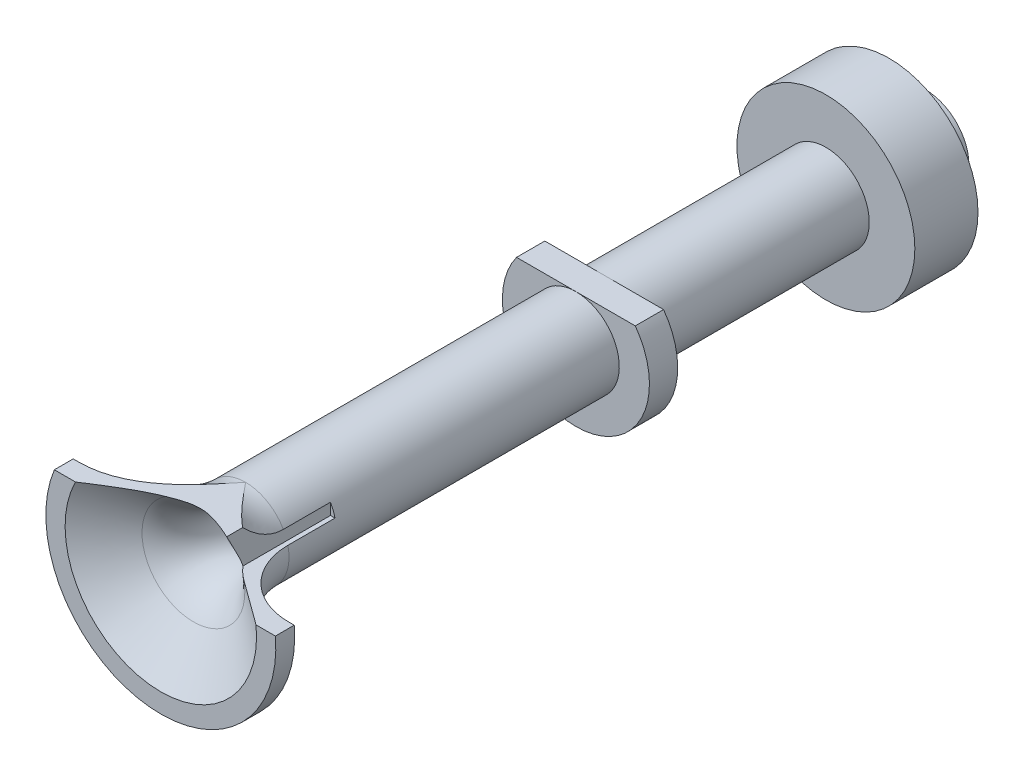
SolidWorks part; units mm, degrees
ref_plane "Спереди" through (0, 0, 0) normal (0, 0, 1) x (1, 0, 0)
ref_plane "Сверху" through (0, 0, 0) normal (0, 1, 0) x (1, 0, 0)
ref_plane "Справа" through (0, 0, 0) normal (1, 0, 0) x (0, 0, -1)
other "Configuration Table"
sketch "Sketch1" plane through (0, 0, 0) normal (1, 0, 0) x (0, 0, -1)
  line L0 (0, 0) -> (15.3, 0) construction
  line L1 (19.1862, 5.0782) -> (19.1862, 6.1)
  line L4 (19.1862, 6.1) -> (20.1862, 6.1)
  line L5 (20.1862, 6.1) -> (20.1862, 5.8)
  line L6 (20.9151, 2.7267) -> (19.1862, 5.0782)
  line L7 (59.7578, 1.3) -> (23.7349, 1.3)
  line L9 (59.7578, 1.3) -> (59.7578, 2.3)
  line L14 (59.7578, 2.3) -> (57.8192, 2.3)
  line L15 (57.8192, 4.7192) -> (54.4692, 4.7192)
  line L20 (54.4692, 2.3) -> (42.7073, 2.3)
  line L21 (42.7073, 3.9) -> (42.7073, 2.3)
  line L22 (41.2073, 3.9) -> (41.2073, 2.3)
  line L23 (42.7073, 3.9) -> (41.2073, 3.9)
  line L24 (41.2073, 2.3) -> (23.6862, 2.3)
  line L29 (54.4692, 2.3) -> (54.4692, 4.7192)
  line L30 (57.8192, 4.7192) -> (57.8192, 2.3)
  arc A0 (20.1862, 5.8) -> (23.6862, 2.3) centre (23.6862, 5.8) ccw
  arc A1 (20.9151, 2.7267) -> (23.7349, 1.3) centre (23.7349, 4.8) ccw
  point P5 (9.4401, -1003.5024)
  point P6 (19.1862, 0)
  point P8 (9.4401, 1010.1)
  point P9 (19.3369, 0)
  point P20 (64.5498, 2.8)
  point P21 (4.5, 2.8)
  point P22 (10.9401, -1003.5024)
  point P23 (10.9401, 1010.1)
  point P26 (27.6401, 10.1)
  point P27 (27.6401, -1000.5024)
  point P30 (26.1401, 10.1)
  point P31 (26.1401, -1000.5024)
revolve "Revolve1" add sketch "Sketch1" angle 360 about L0
sketch "Sketch2" plane through (0, 0, -19.1862) normal (0, 0, 1) x (1, 0, 0)
  line L0 (2, 6) -> (2, 0.5247)
  line L2 (7.7562, 0.5247) -> (7.708, 5.9581)
  line L3 (7.708, 5.9581) -> (2, 6)
  line L6 (2, 0.5247) -> (7.7562, 0.5247)
extrude "Cut-Extrude1" cut sketch "Sketch2" against normal blind 7
sketch "Sketch3" plane through (0, 0, 0) normal (1, 0, 0) x (0, 0, -1)
  line L1 (44.6005, 2.3) -> (17.6669, 2.3)
  line L2 (17.6669, 2.3) -> (17.6669, 8.0267)
  line L3 (17.6669, 8.0267) -> (44.6005, 8.0267)
  line L4 (44.6005, 8.0267) -> (44.6005, 2.3)
extrude "Cut-Extrude2" cut sketch "Sketch3" against normal through all both and the other way through all
